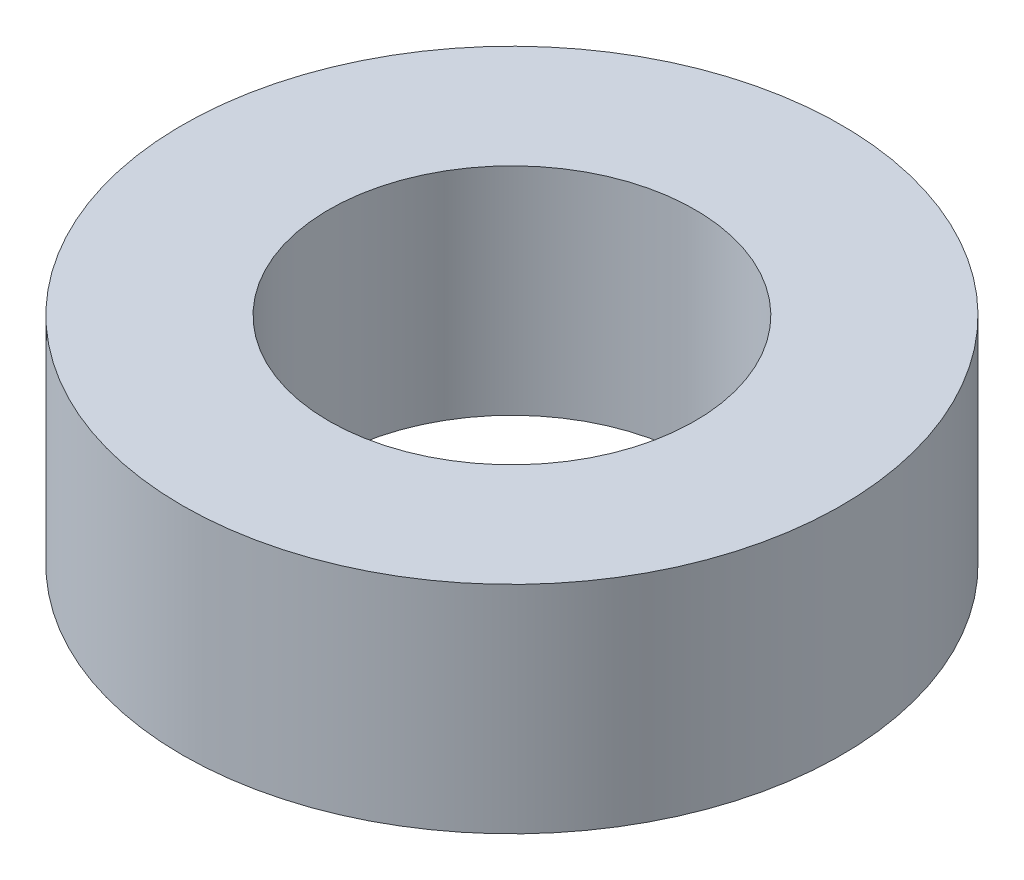
SolidWorks part; units mm, degrees
ref_plane "Front" through (0, 0, 0) normal (0, 0, 1) x (1, 0, 0)
ref_plane "Top" through (0, 0, 0) normal (0, 1, 0) x (1, 0, 0)
ref_plane "Right" through (0, 0, 0) normal (1, 0, 0) x (0, 0, -1)
sketch "Sketch1" plane through (0, 0, 0) normal (0, 1, 0) x (1, 0, 0)
  circle A0 centre (0, 0) radius 4.5
  circle A1 centre (0, 0) radius 2.5
  dimension "D1" = 9
  dimension "D2" = 5
extrude "Boss-Extrude1" add sketch "Sketch1" along normal mid plane 2.95
